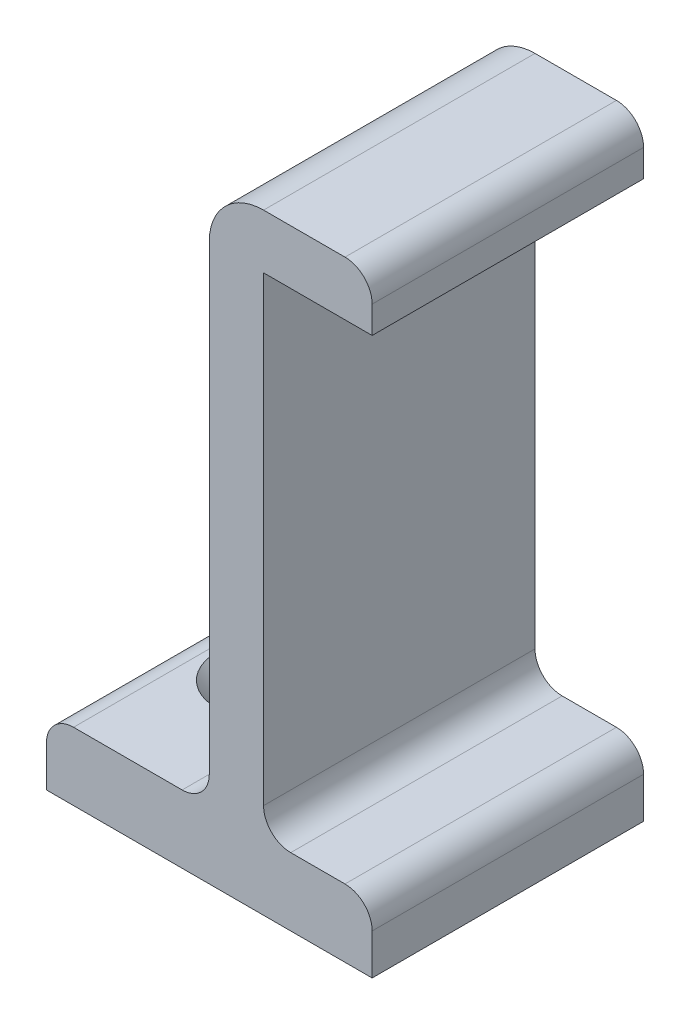
SolidWorks part; units mm, degrees
ref_plane "Ebene vorne" through (0, 0, 0) normal (0, 0, 1) x (1, 0, 0)
ref_plane "Ebene oben" through (0, 0, 0) normal (0, 1, 0) x (1, 0, 0)
ref_plane "Ebene rechts" through (0, 0, 0) normal (1, 0, 0) x (0, 0, -1)
sketch "Skizze1" plane through (0, 0, 0) normal (0, 0, 1) x (1, 0, 0)
  line L0 (-24, 0) -> (0, 0)
  line L1 (-24, 0) -> (-24, 5)
  line L2 (-24, 5) -> (-12, 5)
  line L3 (-12, 5) -> (-12, 45)
  line L4 (-12, 45) -> (0, 45)
  line L5 (0, 45) -> (0, 41)
  line L6 (0, 41) -> (-8, 41)
  line L7 (-8, 41) -> (-8, 5)
  line L8 (-8, 5) -> (0, 5)
  line L9 (0, 5) -> (0, 0)
  line L10 (-8, 5) -> (-12, 5) construction
  dimension "D1" = 41
  dimension "D2" = 5
  dimension "D3" = 4
  dimension "D4" = 8
  dimension "D5" = 12
extrude "Aufsatz-Linear austragen1" add sketch "Skizze1" along normal mid plane 20
sketch "Skizze2" plane through (0, 5, 0) normal (0, 1, 0) x (1, 0, 0)
  line L0 (-18, 0) -> (-12, 0) construction
  line L2 (-18, 0) -> (-24, 0) construction
  line L3 (-24, -10) -> (-24, 10) construction
  line L4 (-12, -10) -> (-12, 10) construction
  circle A0 centre (-18, 0) radius 1.5
  dimension "D1" = 3
extrude "Schnitt-Linear austragen1" cut sketch "Skizze2" against normal through all
chamfer "Fase1" distance 2 angle 45 1 edges at (-19.5, 5, 0)
fillet "Verrundung1" radius 2 5 edges at (-12, 5, 0) (-8, 5, 0) (0, 5, 0) (-24, 5, 0) (0, 45, 0)
fillet "Verrundung2" radius 4 1 edges at (-12, 45, 0)
